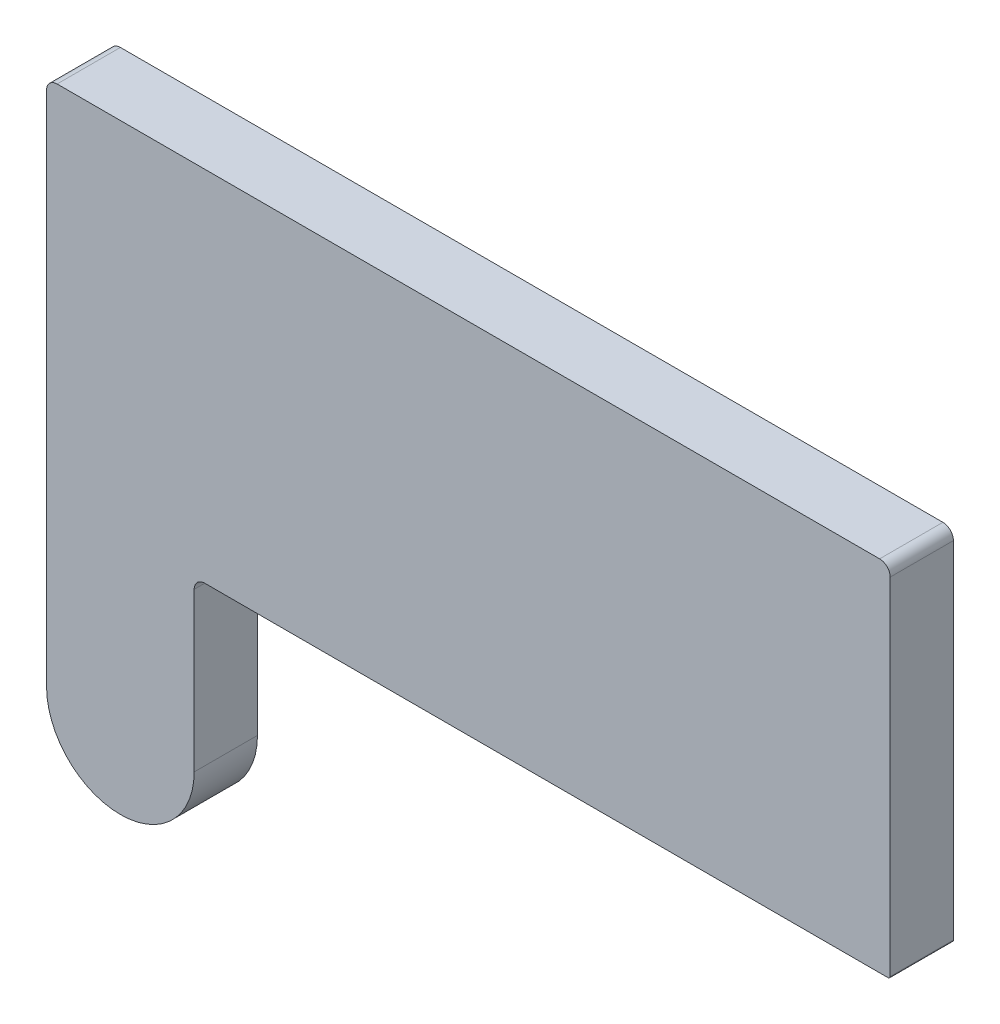
SolidWorks part; units mm, degrees
ref_plane "Front Plane" through (0, 0, 0) normal (0, 0, 1) x (1, 0, 0)
ref_plane "Top Plane" through (0, 0, 0) normal (0, 1, 0) x (1, 0, 0)
ref_plane "Right Plane" through (0, 0, 0) normal (1, 0, 0) x (0, 0, -1)
sketch "Sketch1" plane through (0, 0, 0) normal (0, 0, 1) x (1, 0, 0)
  line L0 (0, 0) -> (0, 24.5)
  line L1 (0.5, 25) -> (28.3397, 25)
  line L2 (36.9669, 8) -> (7.5, 8)
  line L3 (7, 7.5) -> (7, 0)
  line L4 (28.3397, 25) -> (39.5, 25)
  line L5 (40, 24.5) -> (40, 8.1)
  line L6 (39.9, 8) -> (36.9669, 8)
  arc A0 (0, 24.5) -> (0.5, 25) centre (0.5, 24.5) cw
  arc A3 (7, 0) -> (0, 0) centre (3.5, 0) cw
  arc A4 (7.5, 8) -> (7, 7.5) centre (7.5, 7.5) ccw
  arc A5 (39.5, 25) -> (40, 24.5) centre (39.5, 24.5) cw
  arc A6 (40, 8.1) -> (39.9, 8) centre (39.9, 8.1) cw
  point P16 (7, 8)
  dimension "D2" = 40
  dimension "D4" = 0.5
  dimension "D6" = 7
  dimension "D7" = 0.1
  dimension "D9" = 0.5
  dimension "D5" = 0.5
  dimension "D1" = 17
  dimension "D3" = 8
extrude "Body" add sketch "Sketch1" along normal mid plane 3
